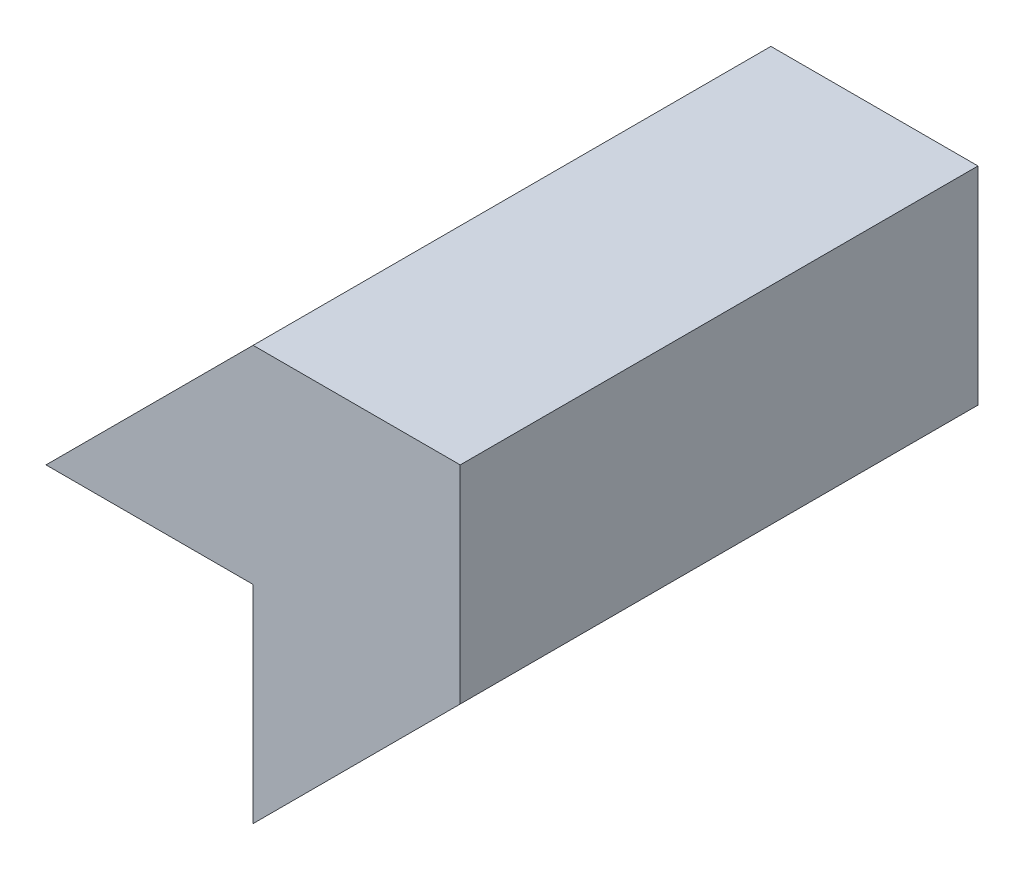
SolidWorks part; units mm, degrees
ref_plane "Front Plane" through (0, 0, 0) normal (0, 0, 1) x (1, 0, 0)
ref_plane "Top Plane" through (0, 0, 0) normal (0, 1, 0) x (1, 0, 0)
ref_plane "Right Plane" through (0, 0, 0) normal (1, 0, 0) x (0, 0, -1)
sketch "Sketch1" plane through (0, 0, 0) normal (0, 0, 1) x (1, 0, 0)
  line L0 (-20, -10) -> (-10, 0)
  line L1 (-10, 0) -> (0, 0)
  line L2 (0, 0) -> (0, -10)
  line L3 (0, -10) -> (-10, -20)
  line L4 (-10, -20) -> (-10, -10)
  line L5 (-10, -10) -> (-20, -10)
  dimension "D1" = 10
  dimension "D2" = 10
  dimension "D3" = 10
  dimension "D4" = 10
extrude "Boss-Extrude1" add sketch "Sketch1" along normal blind 25
